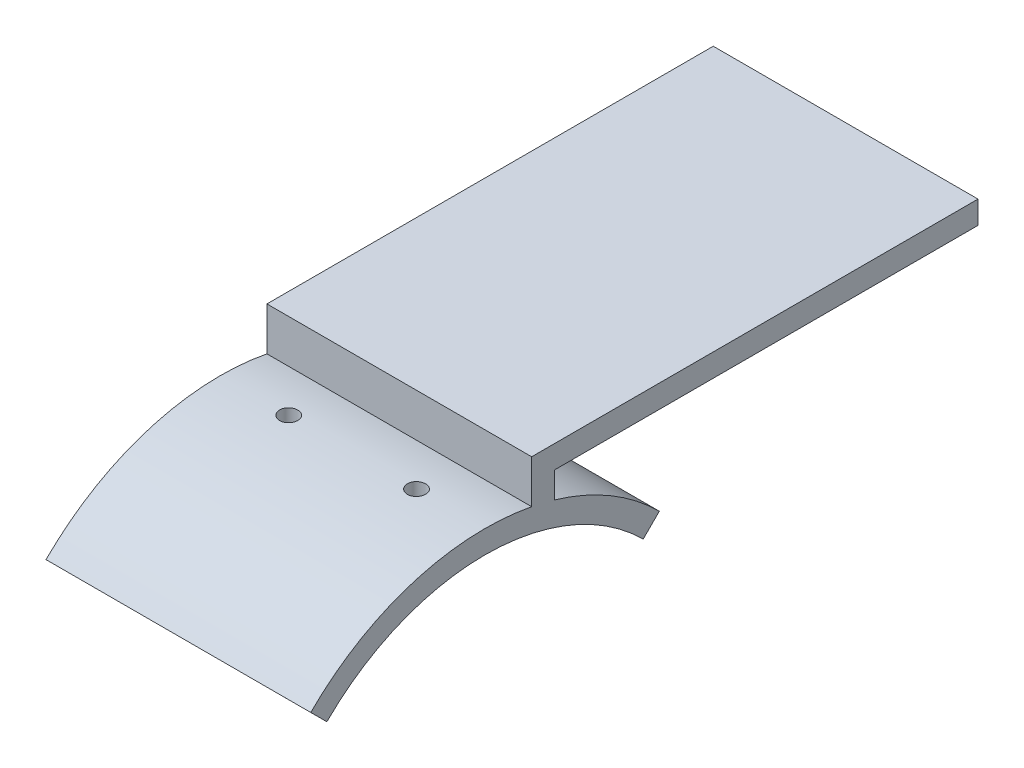
SolidWorks part; units mm, degrees
ref_plane "Front Plane" through (0, 0, 0) normal (0, 0, 1) x (1, 0, 0)
ref_plane "Top Plane" through (0, 0, 0) normal (0, 1, 0) x (1, 0, 0)
ref_plane "Right Plane" through (0, 0, 0) normal (1, 0, 0) x (0, 0, -1)
sketch "Sketch3" plane through (0, 0, 0) normal (1, 0, 0) x (0, 0, -1)
  line L0 (0, 0) -> (0, -49) construction
  line L1 (-34.6482, -14.3518) -> (-38.1838, -10.8162)
  line L2 (0, 0) -> (0, 8.5) construction
  line L3 (34.6482, -14.3518) -> (38.1838, -10.8162)
  line L4 (0, 8.5) -> (108, 8.5) construction
  line L5 (10.2179, 13.5) -> (108, 13.5)
  line L6 (15.2179, 8.5) -> (15.2179, 2.8113)
  line L7 (10.2179, 13.5) -> (10.2179, 4.0245)
  line L8 (10.2179, 13.5) -> (10.2179, 2.8113) construction
  line L9 (15.2179, 13.5) -> (15.2179, 2.8113) construction
  line L10 (0, 13.5) -> (108, 13.5) construction
  line L11 (15.2179, 8.5) -> (108, 8.5)
  line L12 (108, 8.5) -> (108, 13.5)
  arc A0 (-34.6482, -14.3518) -> (34.6482, -14.3518) centre (0, -49) cw
  arc A1 (-38.1838, -10.8162) -> (10.2179, 4.0245) centre (0, -49) cw
  arc A2 (15.2179, 2.8113) -> (38.1838, -10.8162) centre (0, -49) cw
  arc A3 (-38.1838, -10.8162) -> (38.1838, -10.8162) centre (0, -49) cw construction
  dimension "D2" = 8.5
  dimension "D1" = 5
  dimension "D3" = 108
  dimension "D4" = 5
  dimension "D5" = 5
extrude "Boss-Extrude2" add sketch "Sketch3" along normal blind 58
sketch "Sketch4" plane through (0, 0, 0) normal (0, 1, 0) x (1, 0, 0)
  line L0 (0, 0) -> (15, 0) construction
  line L1 (15, 0) -> (29, 0) construction
  line L2 (29, 0) -> (29, 17.9471) construction
  circle A0 centre (15, 0) radius 2
  circle A1 centre (43, 0) radius 2
  dimension "D3" = 4
  dimension "D1" = 15
  dimension "D2" = 14
extrude "Cut-Extrude2" cut sketch "Sketch4" against normal blind 58 and the other way blind 58
